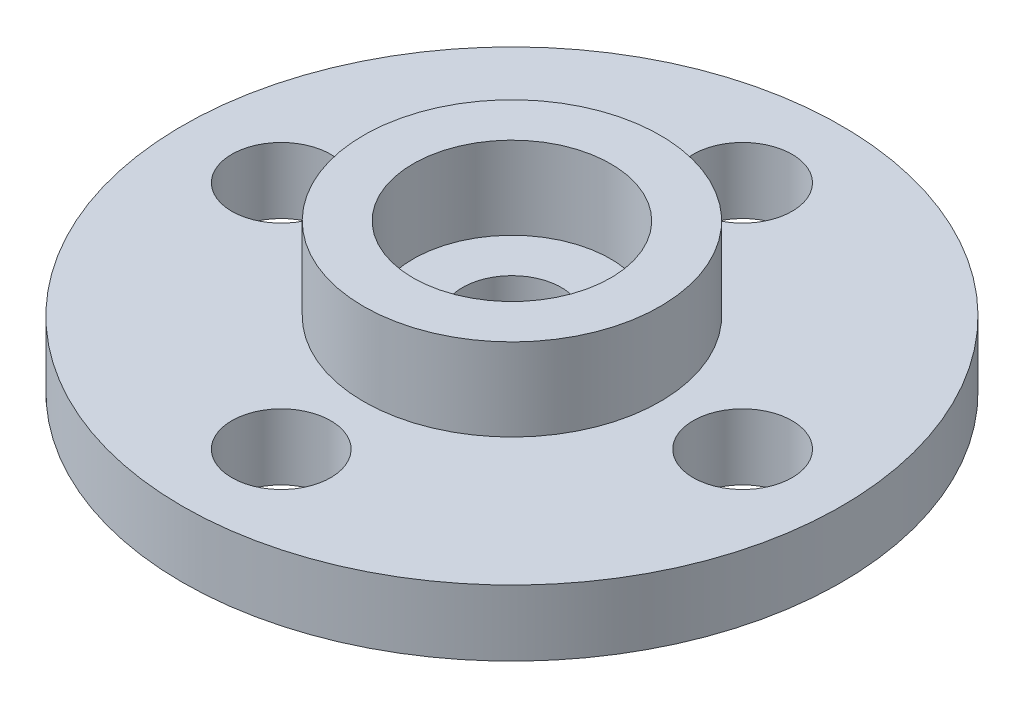
SolidWorks part; units mm, degrees
ref_plane "Front" through (0, 0, 0) normal (0, 0, 1) x (1, 0, 0)
ref_plane "Top" through (0, 0, 0) normal (0, 1, 0) x (1, 0, 0)
ref_plane "Right" through (0, 0, 0) normal (1, 0, 0) x (0, 0, -1)
sketch "Sketch1" plane through (0, 0, 0) normal (0, 1, 0) x (1, 0, 0)
  line L0 (0, 0) -> (0, -7) construction
  circle A0 centre (0, 0) radius 10
  circle A1 centre (0, -7) radius 1.5
  circle A2 centre (-7, 0) radius 1.5
  circle A3 centre (0, 7) radius 1.5
  circle A4 centre (7, 0) radius 1.5
  circle A5 centre (0, 0) radius 1.5
  point P14 (0, 0)
  dimension "D1" = 20
  dimension "D2" = 3
  dimension "D5" = 3
  dimension "D3" = 7
  dimension "D4" = 4
extrude "Boss-Extrude1" add sketch "Sketch1" along normal blind 2
sketch "Sketch2" plane through (0, 2, 0) normal (0, 1, 0) x (1, 0, 0)
  circle A0 centre (0, 0) radius 3
  circle A1 centre (0, 0) radius 4.5
  dimension "D1" = 6
  dimension "D2" = 9
extrude "Boss-Extrude2" add sketch "Sketch2" along normal blind 2.5
